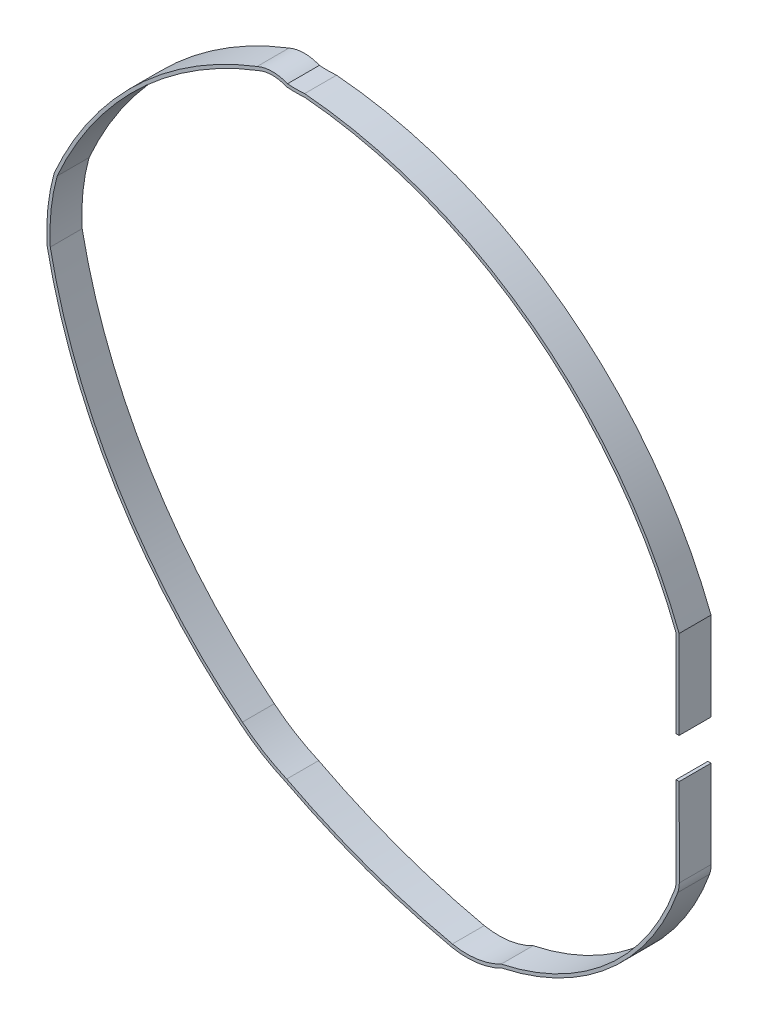
SolidWorks part; units mm, degrees
material "炭素鋼(普通)"
ref_plane "正面" through (0, 0, 0) normal (0, 0, 1) x (1, 0, 0)
ref_plane "平面" through (0, 0, 0) normal (0, 1, 0) x (1, 0, 0)
ref_plane "右側面" through (0, 0, 0) normal (1, 0, 0) x (0, 0, -1)
sketch "ｽｹｯﾁ1" plane through (0, 0, 0) normal (0, 0, 1) x (1, 0, 0)
  line L0 (31.8427, -64.1735) -> (31.8297, -53.1735)
  line L3 (31.8179, -48.1773) -> (31.8179, -37.1773)
  arc A0 (31.8427, -64.1735) -> (31.665, -65.1942) centre (28.8427, -64.1771) cw
  arc A1 (3.7857, -85.0372) -> (9.9126, -84.1583) centre (5.602, -75.9039) ccw
  arc A2 (-14.7442, -2.3513) -> (31.8179, -37.1773) centre (-19.3787, -57.0873) cw
  arc A3 (31.665, -65.1942) -> (9.9126, -84.1583) centre (3.7526, -55.1352) cw
  arc A4 (-16.9875, -77.5076) -> (3.7857, -85.0372) centre (21.6709, -3.2743) ccw
  arc A5 (-22.5434, -74.1057) -> (-16.9875, -77.5076) centre (-7.5317, -55.8267) ccw
  arc A6 (-45.7749, -26.4183) -> (-46.6407, -34.5674) centre (-21.4883, -33.1192) ccw
  arc A7 (-46.6407, -34.5674) -> (-22.5434, -74.1057) centre (19.4934, -21.3731) ccw
  arc A8 (-16.9875, -2.3513) -> (-20.5507, -2.3513) centre (-18.7691, -6.4048) ccw
  arc A9 (-45.7749, -26.4183) -> (-20.5507, -2.3513) centre (-4.2683, -44.6687) cw
  arc A10 (-16.9875, -2.3513) -> (-14.7442, -2.3513) centre (-15.8659, 11.992) ccw
  point P0 (0, 0)
extrude "押し出し-薄板1" add sketch "ｽｹｯﾁ1" along normal blind 4 thin
